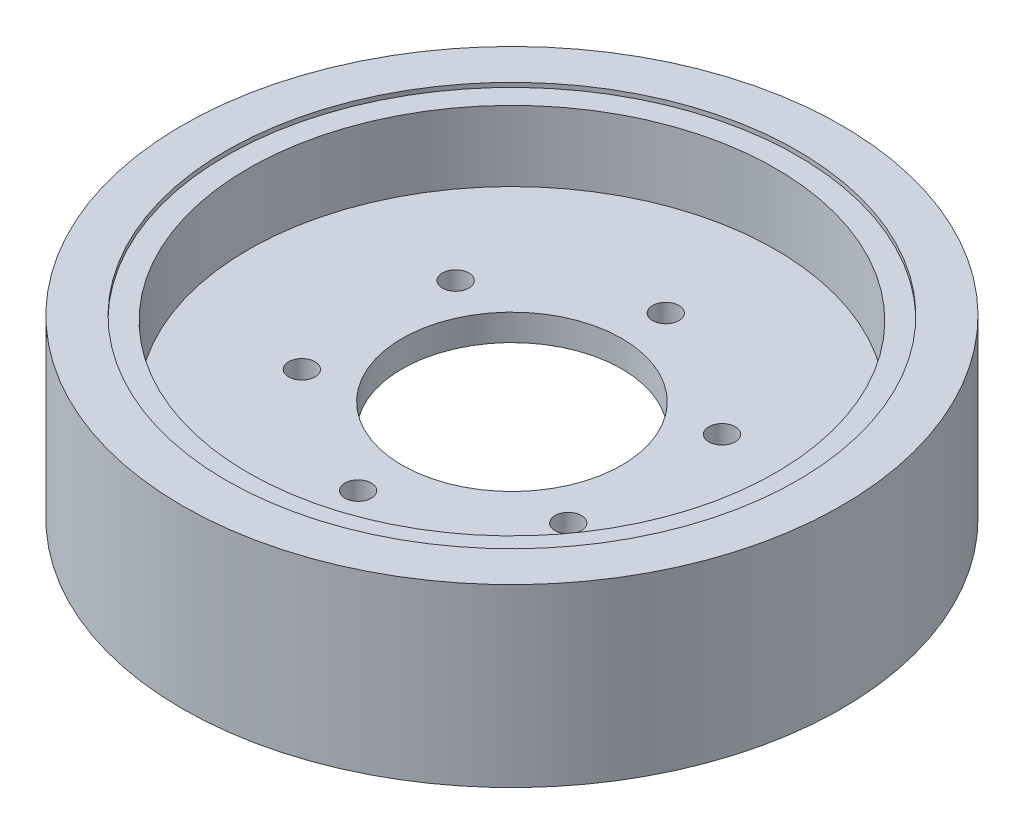
SolidWorks part; units mm, degrees
ref_plane "Front Plane" through (0, 0, 0) normal (0, 0, 1) x (1, 0, 0)
ref_plane "Top Plane" through (0, 0, 0) normal (0, 1, 0) x (1, 0, 0)
ref_plane "Right Plane" through (0, 0, 0) normal (1, 0, 0) x (0, 0, -1)
sketch "Sketch1" plane through (0, 0, 0) normal (0, 1, 0) x (1, 0, 0)
  circle A0 centre (0, 0) radius 75
  dimension "D1" = 150
extrude "Boss-Extrude1" add sketch "Sketch1" along normal blind 40
sketch "Sketch2" plane through (0, 40, 0) normal (0, 1, 0) x (1, 0, 0)
  circle A0 centre (0, 0) radius 60
  dimension "D1" = 120
extrude "Cut-Extrude1" cut sketch "Sketch2" against normal blind 17
sketch "Sketch3" plane through (0, 23, 0) normal (0, 1, 0) x (1, 0, 0)
  circle A0 centre (0, 0) radius 25
  dimension "D1" = 50
extrude "Cut-Extrude2" cut sketch "Sketch3" against normal through all
sketch "Sketch4" plane through (0, 23, 0) normal (0, 1, 0) x (1, 0, 0)
  circle A0 centre (0, 0) radius 35 construction
  circle A1 centre (0, 35) radius 3
  circle A2 centre (30.3109, 17.5) radius 3
  circle A3 centre (30.3109, -17.5) radius 3
  circle A4 centre (0, -35) radius 3
  circle A5 centre (-30.3109, -17.5) radius 3
  circle A6 centre (-30.3109, 17.5) radius 3
  point P17 (0, 0)
  dimension "D1" = 70
  dimension "D2" = 6
  dimension "D3" = 6
extrude "Cut-Extrude3" cut sketch "Sketch4" against normal through all
sketch "Sketch6" plane through (0, 0, 0) normal (0, -1, 0) x (1, 0, 0)
  circle A0 centre (0, 0) radius 60
  dimension "D1" = 120
extrude "Cut-Extrude4" cut sketch "Sketch6" against normal blind 17
sketch "Sketch7" plane through (0, 0, 0) normal (0, -1, 0) x (1, 0, 0)
  circle A0 centre (0, 0) radius 65
  dimension "D1" = 130
extrude "Cut-Extrude5" cut sketch "Sketch7" against normal blind 1
sketch "Sketch8" plane through (0, 40, 0) normal (0, 1, 0) x (1, 0, 0)
  circle A0 centre (0, 0) radius 65
  dimension "D1" = 130
extrude "Cut-Extrude6" cut sketch "Sketch8" against normal blind 1
